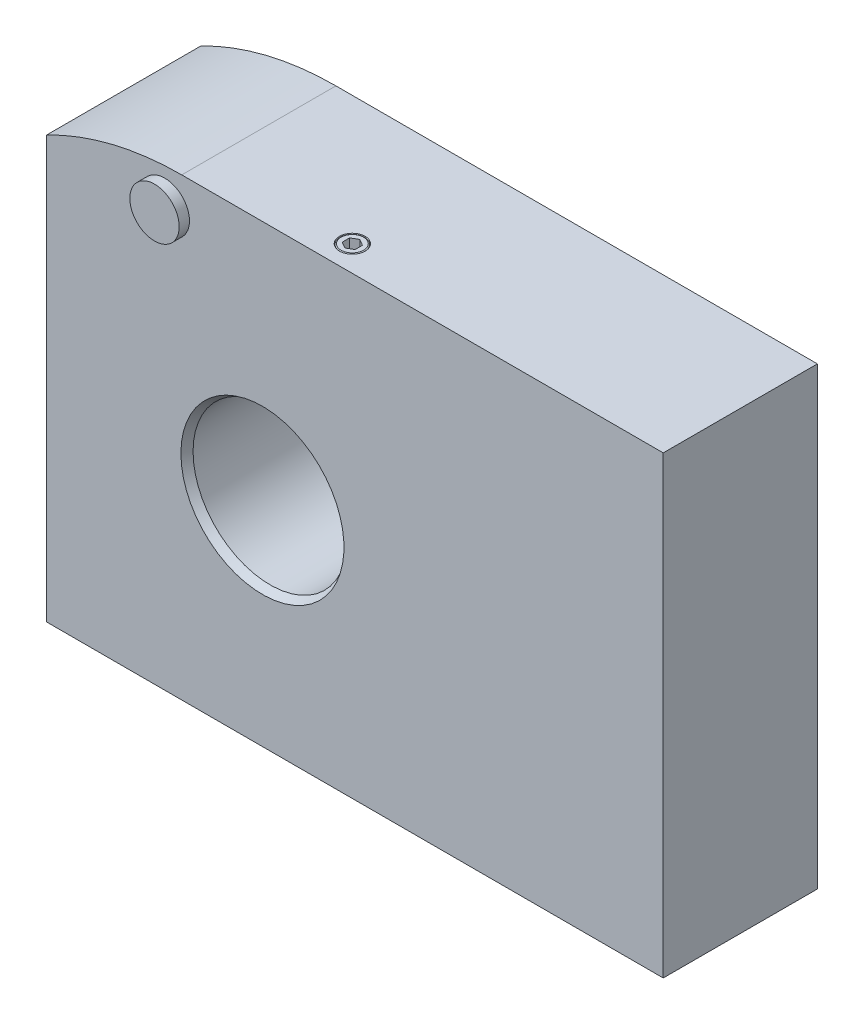
SolidWorks part; units mm, degrees
material "201.0-T43 Insulated Mold Casting (SS)"
ref_plane "Front Plane" through (0, 0, 0) normal (0, 0, 1) x (1, 0, 0)
ref_plane "Top Plane" through (0, 0, 0) normal (0, 1, 0) x (1, 0, 0)
ref_plane "Right Plane" through (0, 0, 0) normal (1, 0, 0) x (0, 0, -1)
ref_plane "Plane1" through (0, 0, 0) normal (0, 0, 1) x (1, 0, 0)
sketch "Sketch1" plane through (0, 0, 0) normal (0, 0, 1) x (1, 0, 0)
  line L0 (0, 0) -> (120, 0)
  line L1 (120, 0) -> (120, 88.5)
  line L2 (120, 88.5) -> (26.3, 88.5)
  line L3 (0, 82.0699) -> (0, 0)
  arc A0 (26.3, 88.5) -> (0, 82.0699) centre (26.3, 31.5) ccw
extrude "Boss-Extrude1" add sketch "Sketch1" against normal blind 30
ref_plane "Plane2" through (42, 0, 0) normal (1, 0, 0) x (0, 0, -1)
sketch "Sketch2" plane through (42, 0, 0) normal (1, 0, 0) x (0, 0, -1)
  line L0 (0, 41.5) -> (0, 57.366)
  line L1 (0, 57.366) -> (1.5, 56.5)
  line L2 (1.5, 56.5) -> (23, 56.5)
  line L3 (23, 56.5) -> (23, 41.5)
  line L4 (23, 41.5) -> (0, 41.5)
  line L5 (23, 41.5) -> (0, 41.5) construction
revolve "Cut-Revolve1" cut sketch "Sketch2" angle 360 about L5
ref_plane "Plane3" through (100.5, 0, 0) normal (1, 0, 0) x (0, 0, -1)
sketch "Sketch3" plane through (100.5, 0, 0) normal (1, 0, 0) x (0, 0, -1)
  line L0 (26.2, 8) -> (29.2, 11)
  line L1 (29.2, 11) -> (29.2, 12.4)
  line L2 (29.2, 12.4) -> (28.6, 13)
  line L3 (28.6, 13) -> (23.2, 13)
  line L4 (23.2, 13) -> (23.2, 13.5)
  line L5 (23.2, 13.5) -> (30, 13.5)
  line L6 (30, 13.5) -> (30, 8)
  line L7 (30, 8) -> (26.2, 8)
  line L8 (30, 8) -> (26.2, 8) construction
revolve "Cut-Revolve2" cut sketch "Sketch3" angle 360 about L8
ref_plane "Plane4" through (16.5, 0, 0) normal (1, 0, 0) x (0, 0, -1)
sketch "Sketch4" plane through (16.5, 0, 0) normal (1, 0, 0) x (0, 0, -1)
  line L0 (26.2, 6.5) -> (29.2, 9.5)
  line L1 (29.2, 9.5) -> (29.2, 10.9)
  line L2 (29.2, 10.9) -> (28.6, 11.5)
  line L3 (28.6, 11.5) -> (23.2, 11.5)
  line L4 (23.2, 11.5) -> (23.2, 12)
  line L5 (23.2, 12) -> (30, 12)
  line L6 (30, 12) -> (30, 6.5)
  line L7 (30, 6.5) -> (26.2, 6.5)
  line L8 (30, 6.5) -> (26.2, 6.5) construction
revolve "Cut-Revolve3" cut sketch "Sketch4" angle 360 about L8
ref_plane "Plane5" through (108.5, 0, 0) normal (1, 0, 0) x (0, 0, -1)
sketch "Sketch5" plane through (108.5, 0, 0) normal (1, 0, 0) x (0, 0, -1)
  line L0 (26.2, 58) -> (29.2, 61)
  line L1 (29.2, 61) -> (29.2, 62.4)
  line L2 (29.2, 62.4) -> (28.6, 63)
  line L3 (28.6, 63) -> (23.2, 63)
  line L4 (23.2, 63) -> (23.2, 63.5)
  line L5 (23.2, 63.5) -> (30, 63.5)
  line L6 (30, 63.5) -> (30, 58)
  line L7 (30, 58) -> (26.2, 58)
  line L8 (30, 58) -> (26.2, 58) construction
revolve "Cut-Revolve4" cut sketch "Sketch5" angle 360 about L8
ref_plane "Plane6" through (13, 0, 0) normal (1, 0, 0) x (0, 0, -1)
sketch "Sketch6" plane through (13, 0, 0) normal (1, 0, 0) x (0, 0, -1)
  line L0 (26.2, 49) -> (29.2, 52)
  line L1 (29.2, 52) -> (29.2, 53.4)
  line L2 (29.2, 53.4) -> (28.6, 54)
  line L3 (28.6, 54) -> (23.2, 54)
  line L4 (23.2, 54) -> (23.2, 54.5)
  line L5 (23.2, 54.5) -> (30, 54.5)
  line L6 (30, 54.5) -> (30, 49)
  line L7 (30, 49) -> (26.2, 49)
  line L8 (30, 49) -> (26.2, 49) construction
revolve "Cut-Revolve5" cut sketch "Sketch6" angle 360 about L8
ref_plane "Plane7" through (0, 0, -30) normal (0, 0, 1) x (1, 0, 0)
sketch "Sketch7" plane through (0, 0, -30) normal (0, 0, 1) x (1, 0, 0)
  line L0 (98, 9.4434) -> (98, 6.5566)
  line L1 (98, 6.5566) -> (100.5, 5.1132)
  line L2 (100.5, 5.1132) -> (103, 6.5566)
  line L3 (103, 6.5566) -> (103, 9.4434)
  line L4 (103, 9.4434) -> (100.5, 10.8868)
  line L5 (100.5, 10.8868) -> (98, 9.4434)
extrude "Cut-Extrude1" cut sketch "Sketch7" along normal blind 3.8
ref_plane "Plane8" through (0, 0, -30) normal (0, 0, 1) x (1, 0, 0)
sketch "Sketch8" plane through (0, 0, -30) normal (0, 0, 1) x (1, 0, 0)
  line L0 (14, 7.9434) -> (14, 5.0566)
  line L1 (14, 5.0566) -> (16.5, 3.6132)
  line L2 (16.5, 3.6132) -> (19, 5.0566)
  line L3 (19, 5.0566) -> (19, 7.9434)
  line L4 (19, 7.9434) -> (16.5, 9.3868)
  line L5 (16.5, 9.3868) -> (14, 7.9434)
extrude "Cut-Extrude2" cut sketch "Sketch8" along normal blind 3.8
ref_plane "Plane9" through (0, 0, -30) normal (0, 0, 1) x (1, 0, 0)
sketch "Sketch9" plane through (0, 0, -30) normal (0, 0, 1) x (1, 0, 0)
  line L0 (106, 59.4434) -> (106, 56.5566)
  line L1 (106, 56.5566) -> (108.5, 55.1132)
  line L2 (108.5, 55.1132) -> (111, 56.5566)
  line L3 (111, 56.5566) -> (111, 59.4434)
  line L4 (111, 59.4434) -> (108.5, 60.8868)
  line L5 (108.5, 60.8868) -> (106, 59.4434)
extrude "Cut-Extrude3" cut sketch "Sketch9" along normal blind 3.8
ref_plane "Plane10" through (0, 0, -30) normal (0, 0, 1) x (1, 0, 0)
sketch "Sketch10" plane through (0, 0, -30) normal (0, 0, 1) x (1, 0, 0)
  line L0 (10.5, 50.4434) -> (10.5, 47.5566)
  line L1 (10.5, 47.5566) -> (13, 46.1132)
  line L2 (13, 46.1132) -> (15.5, 47.5566)
  line L3 (15.5, 47.5566) -> (15.5, 50.4434)
  line L4 (15.5, 50.4434) -> (13, 51.8868)
  line L5 (13, 51.8868) -> (10.5, 50.4434)
extrude "Cut-Extrude4" cut sketch "Sketch10" along normal blind 3.8
ref_plane "Plane11" through (0, 0, -30) normal (0, 0, 1) x (1, 0, 0)
sketch "Sketch11" plane through (0, 0, -30) normal (0, 0, 1) x (1, 0, 0)
  circle A0 centre (80, 21) radius 4.5
extrude "Cut-Extrude5" cut sketch "Sketch11" along normal blind 2.1
ref_plane "Plane12" through (0, 0, -30) normal (0, 0, 1) x (1, 0, 0)
sketch "Sketch12" plane through (0, 0, -30) normal (0, 0, 1) x (1, 0, 0)
  circle A0 centre (40, 21) radius 4.5
extrude "Cut-Extrude6" cut sketch "Sketch12" along normal blind 2.1
ref_plane "Plane13" through (0, 21, 0) normal (0, 1, 0) x (1, 0, 0)
sketch "Sketch13" plane through (0, 21, 0) normal (0, 1, 0) x (1, 0, 0)
  line L0 (100, 30) -> (104, 30)
  line L1 (104, 30) -> (103.3235, 29.3235)
  line L2 (103.3235, 29.3235) -> (103.3235, 8)
  line L3 (103.3235, 8) -> (100, 6.0812)
  line L4 (100, 6.0812) -> (100, 30)
  line L5 (100, 6.0812) -> (100, 30) construction
revolve "Cut-Revolve6" cut sketch "Sketch13" angle 360 about L5
ref_plane "Plane14" through (0, 21, 0) normal (0, 1, 0) x (1, 0, 0)
sketch "Sketch14" plane through (0, 21, 0) normal (0, 1, 0) x (1, 0, 0)
  line L0 (20, 30) -> (24, 30)
  line L1 (24, 30) -> (23.3235, 29.3235)
  line L2 (23.3235, 29.3235) -> (23.3235, 8)
  line L3 (23.3235, 8) -> (20, 6.0812)
  line L4 (20, 6.0812) -> (20, 30)
  line L5 (20, 6.0812) -> (20, 30) construction
revolve "Cut-Revolve7" cut sketch "Sketch14" angle 360 about L5
ref_plane "Plane15" through (0, 0, 0) normal (0, 0, 1) x (1, 0, 0)
sketch "Sketch15" plane through (0, 0, 0) normal (0, 0, 1) x (1, 0, 0)
  circle A0 centre (23, 81.5) radius 4.8
extrude "Boss-Extrude2" add sketch "Sketch15" along normal blind 2
ref_plane "Plane16" through (54.5, 0, 0) normal (1, 0, 0) x (0, 0, -1)
sketch "Sketch16" plane through (54.5, 0, 0) normal (1, 0, 0) x (0, 0, -1)
  line L0 (5, 88.5) -> (2.8066, 88.5)
  line L1 (2.8066, 88.5) -> (2.6122, 88.3878)
  line L2 (2.6122, 88.3878) -> (2.5, 88.5)
  line L3 (2.5, 88.5) -> (2.5, 89.5)
  line L4 (2.5, 89.5) -> (5, 89.5)
  line L5 (5, 89.5) -> (5, 88.5)
  line L6 (5, 89.5) -> (5, 88.5) construction
revolve "Cut-Revolve8" cut sketch "Sketch16" angle 360 about L6
ref_plane "Plane17" through (0, 88.5, 0) normal (0, 1, 0) x (1, 0, 0)
sketch "Sketch17" plane through (0, 88.5, 0) normal (0, 1, 0) x (1, 0, 0)
  line L0 (53.25, 5.7217) -> (53.25, 4.2783)
  line L1 (53.25, 4.2783) -> (54.5, 3.5566)
  line L2 (54.5, 3.5566) -> (55.75, 4.2783)
  line L3 (55.75, 4.2783) -> (55.75, 5.7217)
  line L4 (55.75, 5.7217) -> (54.5, 6.4434)
  line L5 (54.5, 6.4434) -> (53.25, 5.7217)
extrude "Cut-Extrude7" cut sketch "Sketch17" against normal blind 3
